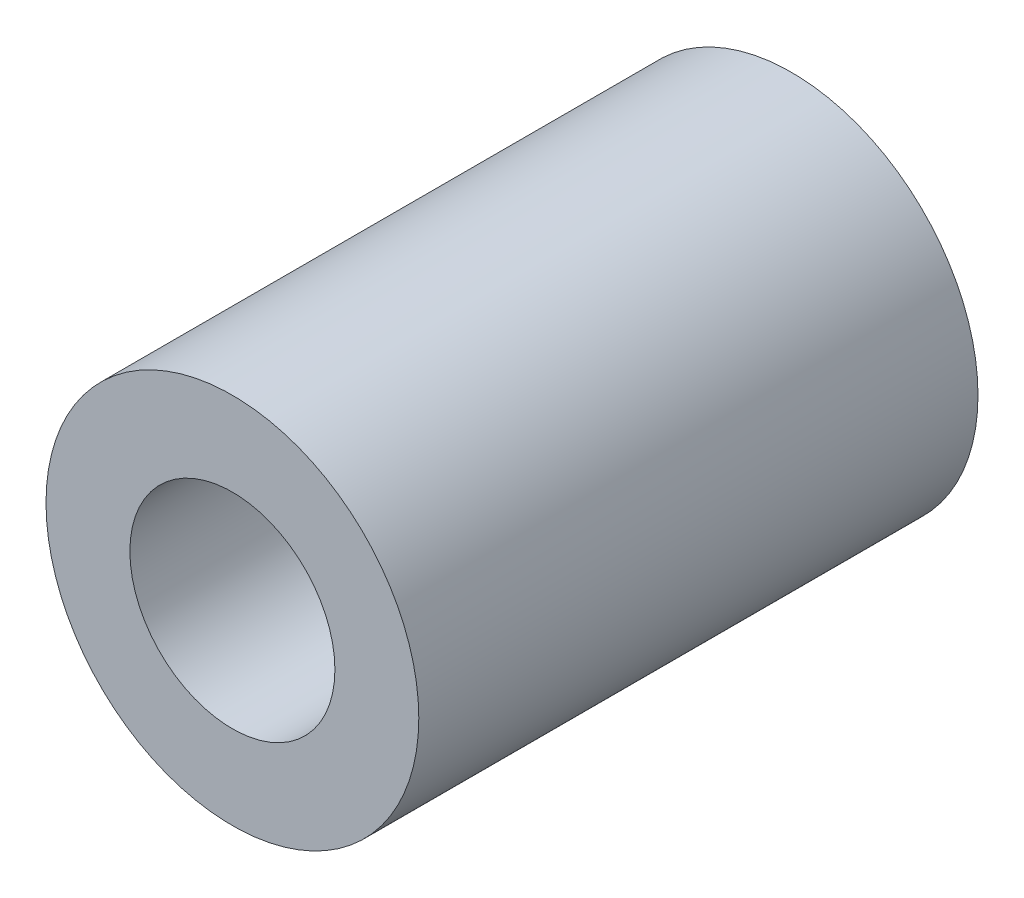
SolidWorks part; units mm, degrees
ref_plane "Plan de face" through (0, 0, 0) normal (0, 0, 1) x (1, 0, 0)
ref_plane "Plan de dessus" through (0, 0, 0) normal (0, 1, 0) x (1, 0, 0)
ref_plane "Plan de droite" through (0, 0, 0) normal (1, 0, 0) x (0, 0, -1)
sketch "Esquisse1" plane through (0, 0, 0) normal (0, 0, 1) x (1, 0, 0)
  circle A0 centre (0, 0) radius 1.1
  circle A1 centre (0, 0) radius 2
  dimension "D1" = 4
  dimension "D2" = 2.2
extrude "Boss.-Extru.1" add sketch "Esquisse1" along normal blind 6
